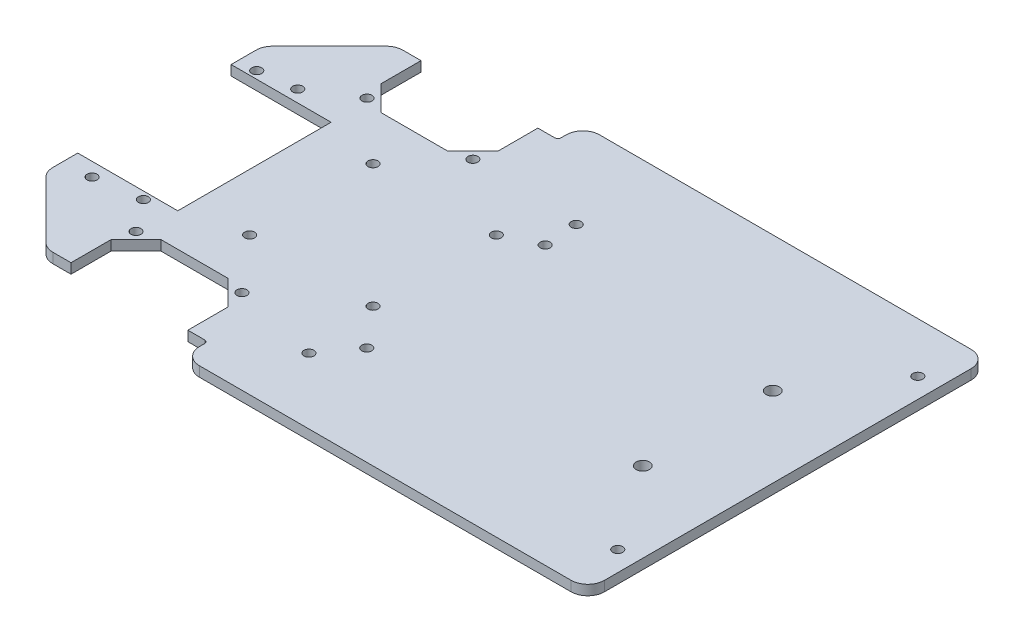
SolidWorks part; units mm, degrees
ref_plane "Front Plane" through (0, 0, 0) normal (0, 0, 1) x (1, 0, 0)
ref_plane "Top Plane" through (0, 0, 0) normal (0, 1, 0) x (1, 0, 0)
ref_plane "Right Plane" through (0, 0, 0) normal (1, 0, 0) x (0, 0, -1)
sketch "Sketch1" plane through (0, 0, 0) normal (0, 1, 0) x (1, 0, 0)
  line L0 (190, 0) -> (0, 0) construction
  line L1 (0, -60) -> (190, -60)
  line L2 (0, -60) -> (0, 60)
  line L3 (0, 60) -> (190, 60)
  line L4 (190, -60) -> (190, 60)
  line L5 (0, -32.5266) -> (27.4734, -60)
  line L6 (30, 23) -> (0, 23) construction
  line L7 (30, 23) -> (30, -23) construction
  line L8 (30, -23) -> (0, -23) construction
  line L9 (0, 23) -> (0, -23)
  line L10 (30, 23) -> (0, -23) construction
  line L11 (30, -23) -> (0, 23) construction
  line L12 (19.9734, -52.5) -> (27.4734, -52.5) construction
  line L13 (68.5266, -52.5) -> (68.5266, -60) construction
  line L14 (35, -33) -> (27.4734, -40.5266) construction
  line L15 (27.4734, -52.5) -> (27.4734, -40.5266) construction
  line L16 (27.4734, -40.5266) -> (27.4734, -52.5) construction
  line L17 (0, 32.5266) -> (27.4734, 60)
  line L18 (35, -33) -> (55, -33) construction
  line L19 (55, -33) -> (62.5266, -40.5266) construction
  line L20 (62.5266, -52.5) -> (68.5266, -52.5) construction
  line L21 (47.5, -37) -> (42.5, -37) construction
  line L22 (45, -37) -> (45, -33) construction
  line L23 (45, -56.5) -> (45, -52.5) construction
  line L24 (39.4, -56.5) -> (50.6, -56.5) construction
  line L25 (27.4734, -52.5) -> (62.5266, -52.5) construction
  line L27 (62.5266, -40.5266) -> (62.5266, -52.5) construction
  point P7 (0, 0)
  point P8 (15, 0)
  dimension "D1" = 120
  dimension "D2" = 190
  dimension "D3" = 30
  dimension "D4" = 23
  dimension "D5" = 10
  dimension "D6" = 20
  dimension "D7" = 45
  dimension "D8" = 45
  dimension "D9" = 45
  dimension "D10" = 7.5
  dimension "D11" = 6
extrude "Boss-Extrude1" add sketch "Sketch1" along normal blind 3 contours L7 L8 L2 L1 L4 L3 L6
sketch "Sketch4" plane through (0, 0, 0) normal (0, 1, 0) x (1, 0, 0)
  line L0 (68.5266, -60) -> (68.5266, -52.5)
  line L1 (68.5266, -52.5) -> (62.5266, -52.5)
  line L2 (62.5266, -52.5) -> (62.5266, -40.5266)
  line L3 (62.5266, -40.5266) -> (55, -33)
  line L4 (55, -33) -> (35, -33)
  line L5 (35, -33) -> (27.4734, -40.5266)
  line L6 (27.4734, -40.5266) -> (27.4734, -52.5)
  line L7 (27.4734, -52.5) -> (19.9734, -52.5)
  line L8 (19.9734, -52.5) -> (27.4734, -60)
  line L9 (27.4734, -60) -> (68.5266, -60)
  line L10 (0, 0) -> (190, 0) construction
  line L11 (190, -60) -> (190, 60) construction
  line L12 (27.4734, 60) -> (68.5266, 60)
  line L13 (19.9734, 52.5) -> (27.4734, 60)
  line L14 (27.4734, 52.5) -> (19.9734, 52.5)
  line L15 (27.4734, 40.5266) -> (27.4734, 52.5)
  line L16 (35, 33) -> (27.4734, 40.5266)
  line L17 (55, 33) -> (35, 33)
  line L18 (62.5266, 40.5266) -> (55, 33)
  line L19 (62.5266, 52.5) -> (62.5266, 40.5266)
  line L20 (68.5266, 52.5) -> (62.5266, 52.5)
  line L21 (68.5266, 60) -> (68.5266, 52.5)
  line L23 (30, 23) -> (0, 23)
  line L24 (30, 23) -> (30, -23)
  line L25 (30, -23) -> (0, -23)
  line L26 (0, 23) -> (0, -23)
extrude "Cut-Extrude1" cut sketch "Sketch4" along normal up to surface (3 mm away) up to face at (72.4911, 3, 0)
fillet "Fillet1" radius 5 8 edges at (190, 1.5, -60) (190, 1.5, 60) (0, 1.5, 32.5266) (0, 1.5, -32.5266) (68.5266, 1.5, 60) (19.9734, 1.5, 52.5) (19.9734, 1.5, -52.5) (68.5266, 1.5, -60)
fillet "Fillet2" radius 1 2 edges at (68.5266, 1.5, -52.5) (68.5266, 1.5, 52.5)
sketch "Sketch5" plane through (0, 0, 0) normal (0, 1, 0) x (1, 0, 0)
  circle A0 centre (47.0626, -18.5) radius 1.5 construction
  circle A1 centre (47.0626, -18.5) radius 1.5
  circle A2 centre (84.0626, -18.5) radius 1.5 construction
  circle A3 centre (84.0626, -18.5) radius 1.5
  circle A4 centre (84.0626, 18.5) radius 1.5 construction
  circle A5 centre (84.0626, 18.5) radius 1.5
  circle A6 centre (47.0626, 18.5) radius 1.5 construction
  circle A7 centre (47.0626, 18.5) radius 1.5
  circle A8 centre (94, 23.2195) radius 1.5 construction
  circle A9 centre (94, 23.2195) radius 1.5
  circle A10 centre (93.3054, 33.2195) radius 1.5 construction
  circle A11 centre (93.3054, 33.2195) radius 1.5
  circle A12 centre (29.1154, 34.642) radius 1.5 construction
  circle A13 centre (60.8846, 34.642) radius 1.5 construction
  circle A14 centre (8.3674, -27.0854) radius 1.5 construction
  circle A15 centre (16.3794, 26.6064) radius 1.5 construction
  circle A16 centre (94, -30.308) radius 1.5 construction
  circle A17 centre (86.6598, -40.308) radius 1.5 construction
  circle A18 centre (29.1154, 34.642) radius 1.5
  circle A19 centre (60.8846, 34.642) radius 1.5
  circle A20 centre (8.3674, -27.0854) radius 1.5
  circle A21 centre (16.3794, 26.6064) radius 1.5
  circle A22 centre (94, -30.308) radius 1.5
  circle A23 centre (86.6598, -40.308) radius 1.5
  circle A24 centre (184, -45) radius 1.5 construction
  circle A25 centre (184, 45) radius 1.5 construction
  circle A26 centre (184, -45) radius 1.5
  circle A27 centre (184, 45) radius 1.5
  circle A28 centre (166, -19.5) radius 2 construction
  circle A29 centre (166, 19.5) radius 2 construction
  circle A30 centre (166, -19.5) radius 2
  circle A31 centre (166, 19.5) radius 2
  circle A32 centre (29.1154, -34.642) radius 1.5 construction
  circle A33 centre (60.8846, -34.642) radius 1.5 construction
  circle A34 centre (29.1154, -34.642) radius 1.5
  circle A35 centre (60.8846, -34.642) radius 1.5
  circle A36 centre (21.9337, -25.25) radius 1.5 construction
  circle A37 centre (5.4397, 25.25) radius 1.5 construction
  circle A38 centre (21.9337, -25.25) radius 1.5
  circle A39 centre (5.4397, 25.25) radius 1.5
extrude "Cut-Extrude2" cut sketch "Sketch5" along normal up to surface (3 mm away) up to face at (55.2686, 3, 0)
